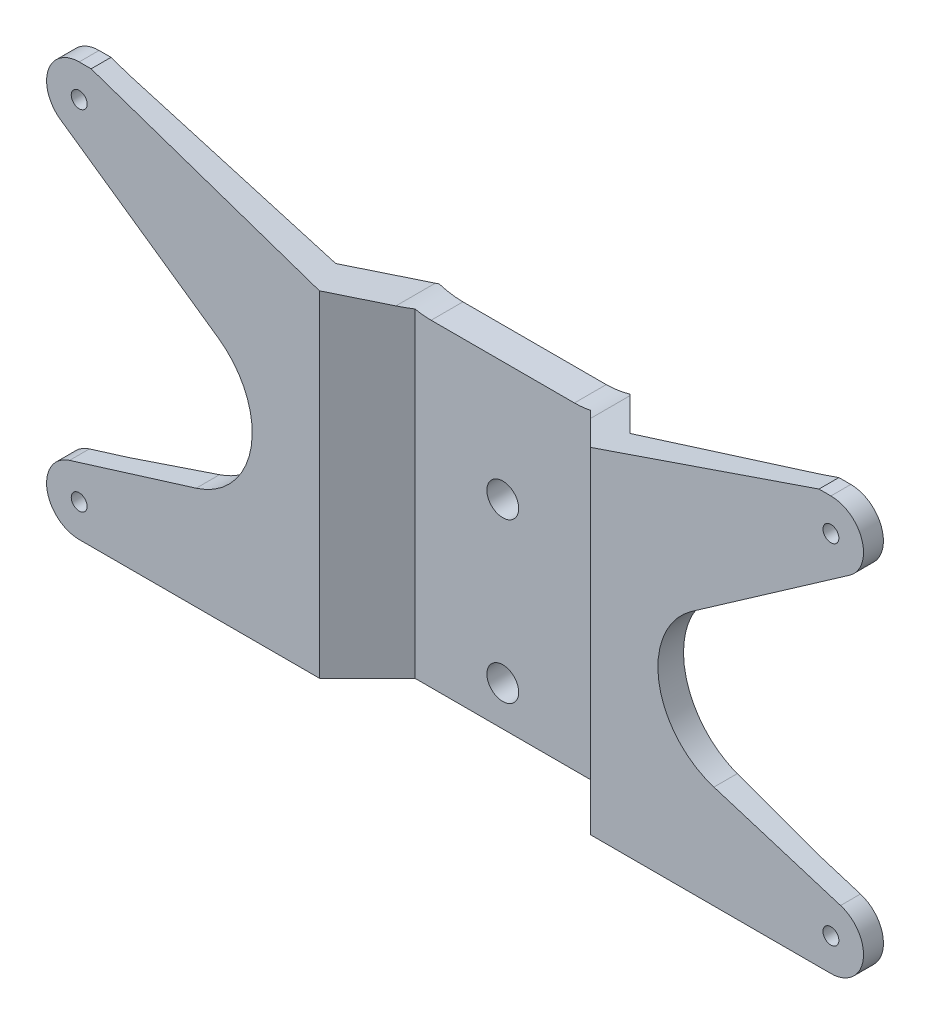
SolidWorks part; units mm, degrees
ref_plane "Front Plane" through (0, 0, 0) normal (0, 0, 1) x (1, 0, 0)
ref_plane "Top Plane" through (0, 0, 0) normal (0, 1, 0) x (1, 0, 0)
ref_plane "Right Plane" through (0, 0, 0) normal (1, 0, 0) x (0, 0, -1)
sketch "Sketch1" plane through (0, 0, 0) normal (0, 1, 0) x (1, 0, 0)
  line L0 (0, 0) -> (0, -4)
  line L1 (0, -4) -> (11.0503, -4)
  line L2 (11.0503, -4) -> (17.0503, -10)
  line L3 (17.0503, -10) -> (51.5, -10)
  line L4 (51.5, -10) -> (51.5, -7.5)
  line L6 (18.5, -6.5) -> (12, 0)
  line L7 (12, 0) -> (0, 0)
  line L8 (51.5, -7.5) -> (43.5, -7.5)
  line L9 (43.5, -7.5) -> (18.5, -6.5)
  point P10 (18.7167, -6.7167)
  dimension "D1" = 51.5
  dimension "D2" = 4
  dimension "D3" = 3.5
  dimension "D4" = 2.5
  dimension "D5" = 10
  dimension "D6" = 12
  dimension "D7" = 45
  dimension "D8" = 3.5
  dimension "D9" = 8
extrude "Boss-Extrude1" add sketch "Sketch1" along normal blind 52
sketch "Sketch2" plane through (0, 0, 10) normal (0, 0, 1) x (1, 0, 0)
  line L0 (45.75, 52) -> (0, 52)
  line L1 (47.25, 4.1) -> (47.25, 47.9) construction
  line L2 (51.5, 26) -> (-19.0799, 26) construction
  line L3 (51.5, 52) -> (51.5, 0) construction
  line L4 (0, 52) -> (0, 0) construction
  line L5 (17.0503, 52) -> (51.5, 52) construction
  line L6 (49.5971, 44.5383) -> (29.7754, 30.6994)
  line L7 (17.0503, 0) -> (51.5, 0) construction
  line L8 (32.5415, 12.9477) -> (48.463, 8.0165)
  line L9 (47.25, 52) -> (51.5, 52)
  line L10 (51.5, 52) -> (51.5, 0)
  line L11 (51.5, 0) -> (47.25, 0)
  line L13 (0, 52) -> (0, 40)
  line L14 (0, 40) -> (9.0065, 40)
  line L15 (12.2431, 40.5383) -> (45.75, 52)
  line L16 (0, 0) -> (11.0503, 0) construction
  circle A0 centre (47.25, 47.9) radius 1
  circle A1 centre (47.25, 4.1) radius 1
  arc A2 (47.25, 52) -> (49.5971, 44.5383) centre (47.25, 47.9) cw
  arc A3 (29.7754, 30.6994) -> (32.5415, 12.9477) centre (35.5, 22.5) ccw
  arc A4 (47.25, 0) -> (48.463, 8.0165) centre (47.25, 4.1) ccw
  arc A5 (9.0065, 40) -> (12.2431, 40.5383) centre (9.0065, 50) ccw
  point P8 (47.25, 26)
  dimension "D3" = 2
  dimension "D4" = 10
  dimension "D5" = 16
  dimension "D7" = 10
  dimension "D1" = 43.8
  dimension "D2" = 47.25
  dimension "D6" = 3.5
  dimension "D8" = 40
  dimension "D9" = 9.0065
  dimension "D10" = 1.5
extrude "Cut-Extrude1" cut sketch "Sketch2" against normal through all
mirror "Mirror1" about plane through (0, 52, 0) normal (1, 0, 0) of bodies 102
sketch "Sketch3" plane through (0, 0, 4) normal (0, 0, 1) x (1, 0, 0)
  line L0 (0, 0) -> (0, 57.5154) construction
  line L1 (-11.0503, 0) -> (11.0503, 0) construction
  circle A0 centre (0, 5) radius 2
  circle A1 centre (0, 25) radius 2
  dimension "D2" = 4
  dimension "D1" = 5
  dimension "D3" = 20
extrude "Cut-Extrude2" cut sketch "Sketch3" against normal through all
